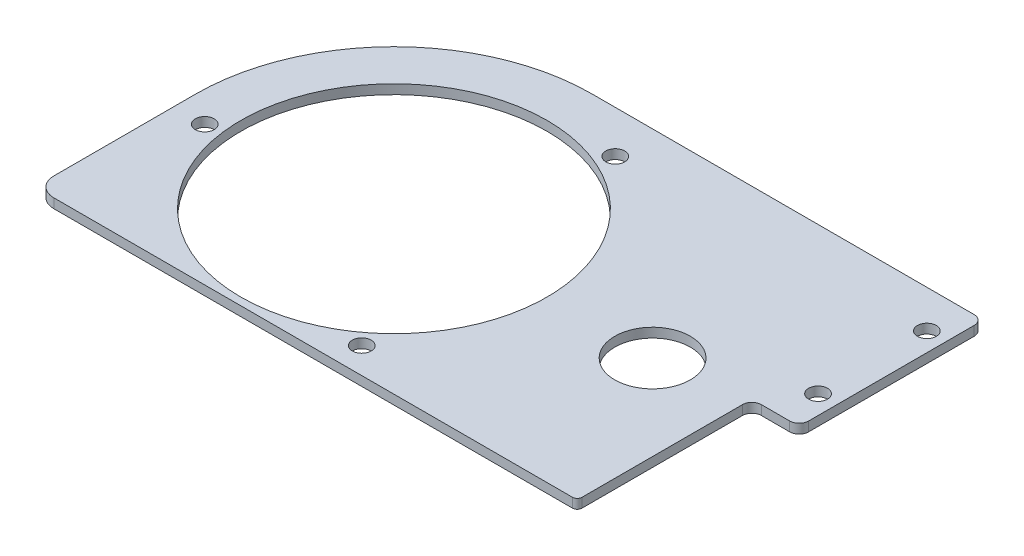
SolidWorks part; units mm, degrees
ref_plane "Front Plane" through (0, 0, 0) normal (0, 0, 1) x (1, 0, 0)
ref_plane "Top Plane" through (0, 0, 0) normal (0, 1, 0) x (1, 0, 0)
ref_plane "Right Plane" through (0, 0, 0) normal (1, 0, 0) x (0, 0, -1)
sketch "Sketch1" plane through (0, 0, 0) normal (0, 1, 0) x (1, 0, 0)
  line L0 (0, 114.3) -> (0, -101.6) construction
  line L1 (256.5211, 133.3689) -> (0, 133.3689)
  line L2 (262.8711, 127.0189) -> (262.8711, 15.8008)
  line L3 (227.9555, -107.9311) -> (-120.6689, -107.9311)
  line L4 (-133.3689, 0) -> (-133.3689, -95.2311)
  line L5 (237.4711, 9.4508) -> (256.5211, 9.4508)
  line L6 (250.1711, 9.4508) -> (250.1711, 133.3689) construction
  line L7 (0, 0) -> (-133.3689, 0) construction
  line L8 (0, 0) -> (-133.3689, -3.0078) construction
  line L11 (231.1211, -104.7655) -> (231.1211, 3.1008)
  circle A0 centre (0, 0) radius 102.87
  circle A1 centre (0, 0) radius 114.3 construction
  circle A2 centre (-112.7386, -14.375) radius 6.35
  arc A3 (237.4711, 9.4508) -> (231.1211, 3.1008) centre (237.4711, 3.1008) ccw
  arc A4 (-133.3689, 0) -> (0, 133.3689) centre (0, 0) cw
  circle A5 centre (43.9202, 104.822) radius 6.35
  circle A6 centre (68.8184, -90.447) radius 6.35
  arc A7 (-120.6689, -107.9311) -> (-133.3689, -95.2311) centre (-120.6689, -95.2311) cw
  arc A8 (227.9555, -107.9311) -> (231.1211, -104.7655) centre (227.9555, -104.7655) ccw
  arc A9 (262.8711, 15.8008) -> (256.5211, 9.4508) centre (256.5211, 15.8008) cw
  arc A10 (256.5211, 133.3689) -> (262.8711, 127.0189) centre (256.5211, 127.0189) cw
  circle A11 centre (250.1711, 107.9689) radius 6.35
  circle A12 centre (250.1711, 34.8508) radius 6.35
  circle A13 centre (-112.7386, -14.375) radius 6.35 construction
  point P0 (0, 0)
  point P11 (0, 0)
  point P12 (246.9961, 9.4508)
  point P32 (231.1211, -107.9311)
  point P46 (0, 0)
  dimension "D3" = 205.74
  dimension "D5" = 228.6
  dimension "D6" = 12.7
  dimension "D7" = 123.9181
  dimension "D8" = 133.3689
  dimension "D11" = 31.75
  dimension "D12" = 25.4
  dimension "D14" = 12.7
  dimension "D9" = 6.35
  dimension "D10" = 12.7
  dimension "D2" = 117.3819
  dimension "D4" = 113.6514
  dimension "D13" = 12.7
  dimension "D15" = 25.4
  dimension "D16" = 396.24
  dimension "D17" = 3
extrude "Boss-Extrude1" add sketch "Sketch1" along normal blind 6.35
sketch "Sketch3" plane through (0, 6.35, 0) normal (0, 1, 0) x (1, 0, 0)
  line L0 (73.0061, 133.3689) -> (73.0061, -107.9311) construction
  line L5 (382.3904, 12.7189) -> (-202.4477, 12.7189) construction
  line L6 (333.3561, -152.3811) -> (-187.3439, -152.3811)
  line L7 (333.3561, -152.3811) -> (333.3561, 177.8189)
  line L8 (333.3561, 177.8189) -> (-187.3439, 177.8189)
  line L9 (-187.3439, -152.3811) -> (-187.3439, 177.8189)
  line L10 (333.3561, -152.3811) -> (-187.3439, 177.8189) construction
  line L11 (333.3561, 177.8189) -> (-187.3439, -152.3811) construction
  line L26 (262.8711, 15.8008) -> (262.8711, 127.0189) construction
  line L27 (-133.3689, 0) -> (-133.3689, -95.2311) construction
  line L28 (-120.6689, -107.9311) -> (227.9555, -107.9311) construction
  line L29 (256.5211, 133.3689) -> (0, 133.3689) construction
  line L30 (262.8711, 15.8008) -> (262.8711, 127.0189)
  line L31 (-133.3689, 0) -> (-133.3689, -95.2311)
  line L32 (-120.6689, -107.9311) -> (227.9555, -107.9311)
  line L33 (256.5211, 133.3689) -> (0, 133.3689)
  point P1 (73.0061, 12.7189)
  dimension "D1" = 520.7
  dimension "D2" = 206.375
  dimension "D3" = 330.2
  dimension "D4" = 120.65
  dimension "D7" = 396.24
  dimension "D8" = 241.3
sketch "Sketch5" plane through (0, 0, 0) normal (0, 1, 0) x (1, 0, 0)
  line L0 (0, 0) -> (197.6982, -56.1867) construction
  circle A1 centre (28.1907, -8.0119) radius 11.176 construction
sketch "Sketch6" plane through (0, 0, 0) normal (0, 1, 0) x (1, 0, 0)
  line L0 (6.35, 0) -> (5.207, 0) construction
  line L1 (0, 0) -> (229.3291, 0) construction
  circle A0 centre (173.8109, 0) radius 25.4
  dimension "D1" = 50.8
extrude "Cut-Extrude1" cut sketch "Sketch6" along normal blind 28.448
